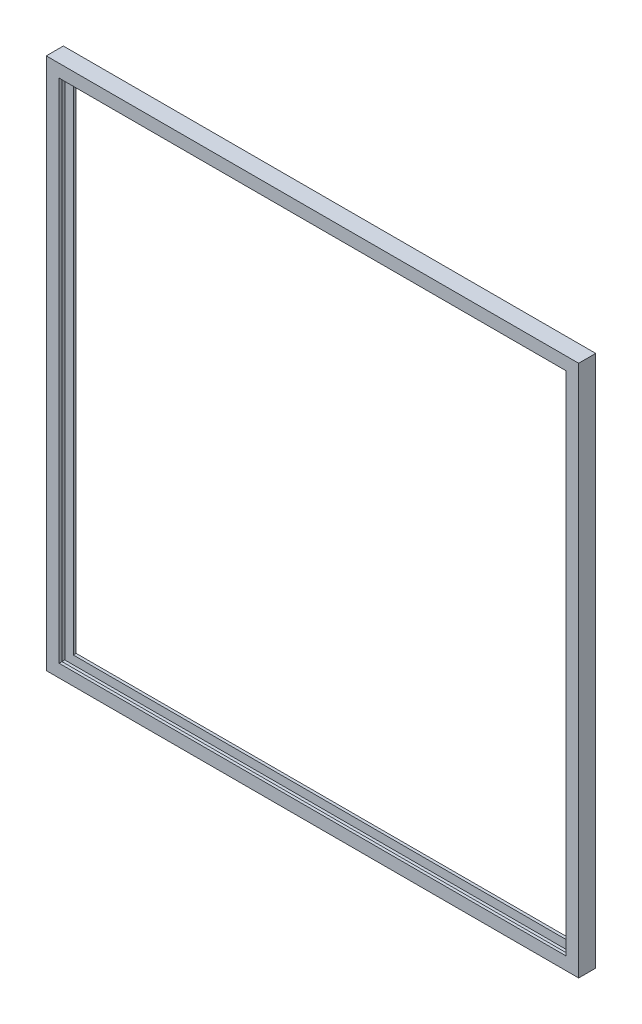
SolidWorks part; units mm, degrees
material "ABS"
ref_plane "Front Plane" through (0, 0, 0) normal (0, 0, 1) x (1, 0, 0)
ref_plane "Top Plane" through (0, 0, 0) normal (0, 1, 0) x (1, 0, 0)
ref_plane "Right Plane" through (0, 0, 0) normal (1, 0, 0) x (0, 0, -1)
sketch "Sketch1" plane through (0, 0, 0) normal (1, 0, 0) x (0, 0, -1)
  line L0 (-9.525, 14.2875) -> (-9.525, 0)
  line L1 (-9.525, 0) -> (9.525, 0)
  line L2 (9.525, 0) -> (9.525, 14.2875)
  line L3 (9.525, 14.2875) -> (6.35, 14.2875)
  line L4 (6.35, 14.2875) -> (6.35, 4.7625)
  line L5 (6.35, 4.7625) -> (-6.35, 4.7625)
  line L6 (-6.35, 4.7625) -> (-6.35, 14.2875)
  line L7 (-6.35, 14.2875) -> (-9.525, 14.2875)
  point P9 (0, 0)
  dimension "D1" = 9.525
  dimension "D2" = 19.05
  dimension "D3" = 4.7625
  dimension "D4" = 3.175
  dimension "D5" = 3.175
sketch "Sketch2" plane through (0, 0, 0) normal (0, 0, 1) x (1, 0, 0)
  line L1 (-296.8625, 593.725) -> (296.8625, 593.725)
  line L2 (-296.8625, 593.725) -> (-296.8625, 0)
  line L3 (-296.8625, 0) -> (296.8625, 0)
  line L4 (296.8625, 593.725) -> (296.8625, 0)
  line L5 (-296.8625, 593.725) -> (296.8625, 0) construction
  line L6 (-296.8625, 0) -> (296.8625, 593.725) construction
  point P0 (0, 296.8625)
  point P5 (50.3255, 356.4587)
  point P6 (0, 0)
  dimension "D1" = 593.725
  dimension "D2" = 593.725
sweep "Sweep1" add profiles "Sketch1" path "Sketch2"
